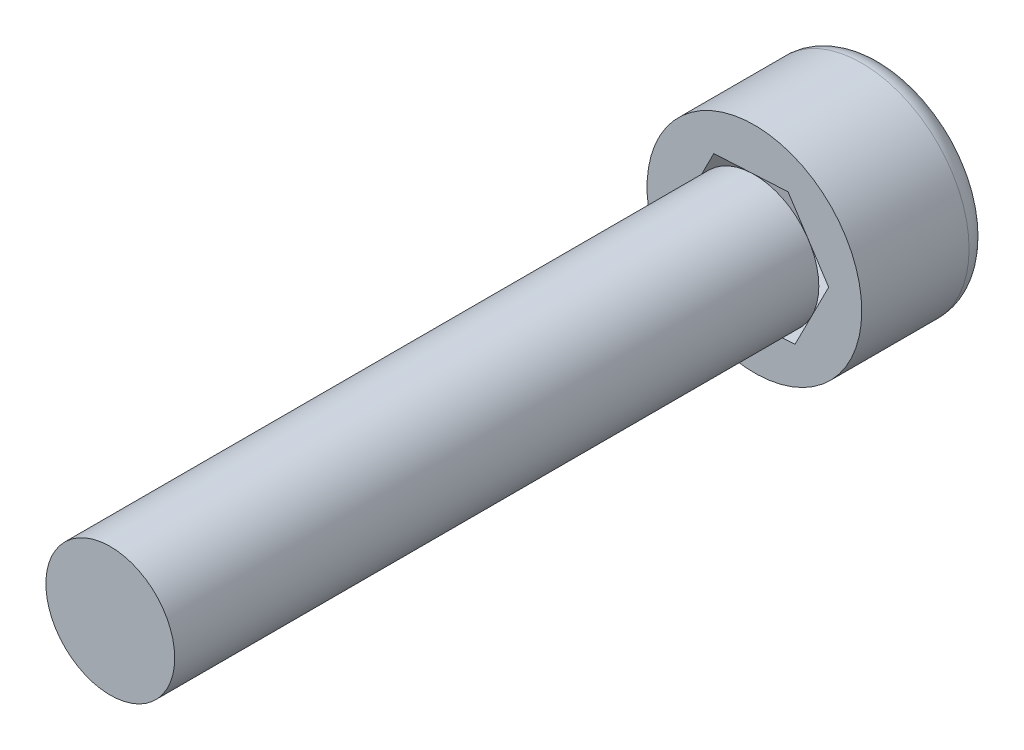
SolidWorks part; units mm, degrees
ref_plane "Front Plane" through (0, 0, 0) normal (0, 0, 1) x (1, 0, 0)
ref_plane "Top Plane" through (0, 0, 0) normal (0, 1, 0) x (1, 0, 0)
ref_plane "Right Plane" through (0, 0, 0) normal (1, 0, 0) x (0, 0, -1)
sketch "Sketch1" plane through (0, 0, 0) normal (0, 0, 1) x (1, 0, 0)
  circle A0 centre (0, 0) radius 2.5
  dimension "D1" = 5
extrude "Boss-Extrude1" add sketch "Sketch1" along normal blind 3
sketch "Sketch2" plane through (0, 0, 3) normal (0, 0, 1) x (1, 0, 0)
  circle A0 centre (0, 0) radius 1.5
  dimension "D1" = 3
extrude "Boss-Extrude2" add sketch "Sketch2" along normal blind 15
sketch "Sketch3" plane through (0, 0, 0) normal (0, 0, -1) x (-1, 0, 0)
  line L1 (0.7845, -1.5442) -> (1.7296, -0.0927)
  line L2 (1.7296, -0.0927) -> (0.9451, 1.4515)
  line L3 (0.9451, 1.4515) -> (-0.7845, 1.5442)
  line L4 (-0.7845, 1.5442) -> (-1.7296, 0.0927)
  line L5 (-1.7296, 0.0927) -> (-0.9451, -1.4515)
  line L6 (-0.9451, -1.4515) -> (0.7845, -1.5442)
  circle A0 centre (0, 0) radius 1.5 construction
  dimension "D1" = 3
extrude "Cut-Extrude1" cut sketch "Sketch3" against normal blind 3
fillet "Fillet1" radius 0.5 1 edges at (2.5, 0, 0)
